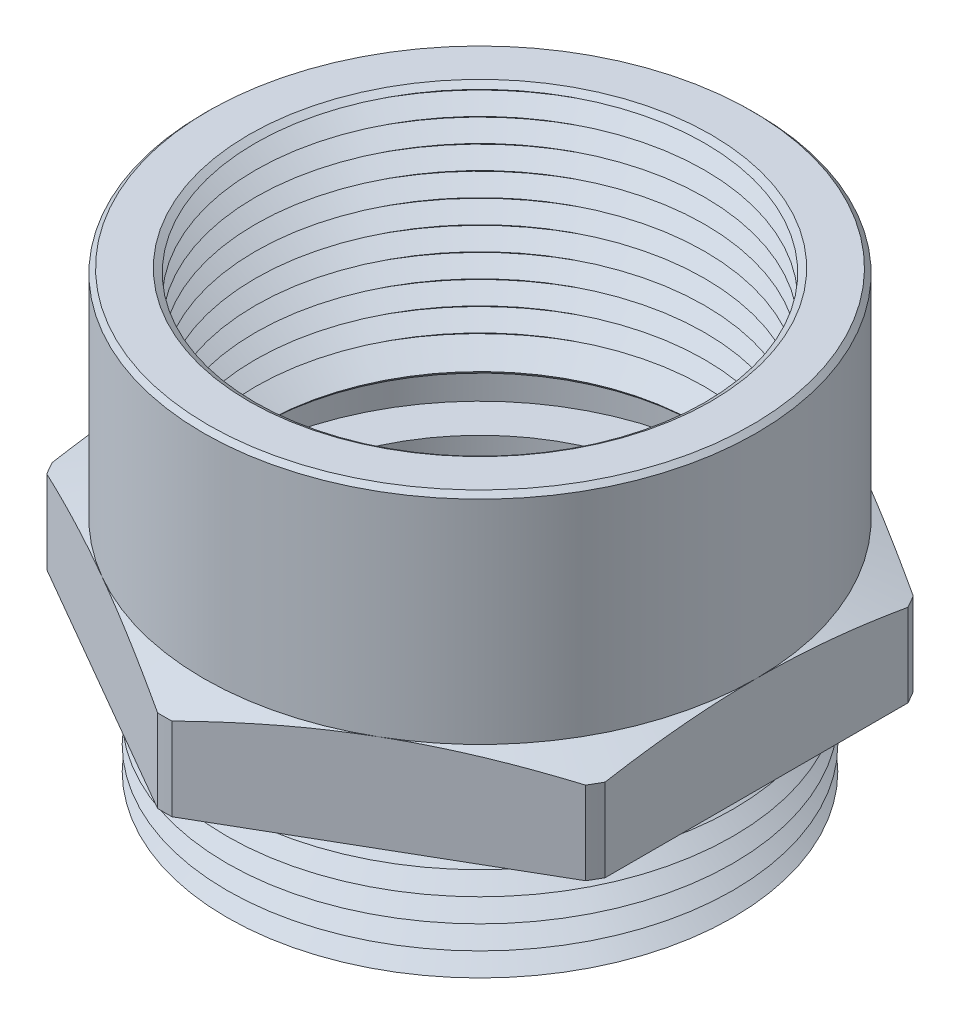
SolidWorks part; units mm, degrees
ref_plane "Front Plane" through (0, 0, 0) normal (0, 0, 1) x (1, 0, 0)
ref_plane "Top Plane" through (0, 0, 0) normal (0, 1, 0) x (1, 0, 0)
ref_plane "Right Plane" through (0, 0, 0) normal (1, 0, 0) x (0, 0, -1)
sketch "Sketch1" plane through (0, 0, 0) normal (0, 0, 1) x (1, 0, 0)
  line L0 (0, 0) -> (0, 68.999) construction
  line L1 (11.2776, 0) -> (13.9174, 0)
  line L2 (13.9174, 0) -> (14.097, 6.858)
  line L3 (14.097, 6.858) -> (17.084, 6.858)
  line L4 (17.084, 6.858) -> (17.084, 12.1107)
  line L5 (17.084, 12.1107) -> (14.986, 12.1107)
  line L6 (14.986, 12.1107) -> (14.986, 23.876)
  line L7 (14.986, 23.876) -> (12.1247, 23.876)
  line L8 (11.7729, 10.4394) -> (12.1247, 23.876)
  line L9 (11.7729, 10.4394) -> (13.5388, 10.4394)
  line L10 (13.5388, 10.4394) -> (13.5388, 8.0518)
  line L11 (13.5388, 8.0518) -> (11.2776, 8.0518)
  line L12 (11.2776, 8.0518) -> (11.2776, 0)
  dimension "D1" = 1.5
  dimension "D2" = 1.5
  dimension "A" = 28.194
  dimension "0.8A" = 22.5552
  dimension "B" = 23.5458
  dimension "T" = 6.858
  dimension "H" = 23.876
  dimension "0.22H" = 5.2527
  dimension "W1" = 34.1681
  dimension "1.1B" = 27.0777
  dimension "T+.05H" = 8.0518
  dimension "W" = 29.972
  dimension ".1H" = 2.3876
revolve "Revolve1" add sketch "Sketch1" angle 360 about L0
sketch "Sketch2" plane through (0, 6.858, 0) normal (0, -1, 0) x (1, 0, 0)
  line L1 (14.986, 8.6522) -> (0, 17.3043)
  line L2 (0, 17.3043) -> (-14.986, 8.6522)
  line L3 (-14.986, 8.6522) -> (-14.986, -8.6522)
  line L4 (-14.986, -8.6522) -> (0, -17.3043)
  line L5 (0, -17.3043) -> (14.986, -8.6522)
  line L6 (14.986, -8.6522) -> (14.986, 8.6522)
  circle A0 centre (0, 0) radius 14.986 construction
  dimension "Wr" = 29.972
extrude "Cut-Extrude1" cut sketch "Sketch2" against normal through all flip side to cut
sketch "Sketch4" plane through (0, 12.1107, 0) normal (0, 1, 0) x (-1, 0, 0)
  circle A0 centre (0, 0) radius 14.986 construction
  circle A1 centre (0, 0) radius 14.986
extrude "Cut-Extrude3" cut sketch "Sketch4" against normal blind 1.27 draft 70 flip side to cut
chamfer "Chamfer2" distance 0.254 angle 45 1 edges at (0, 10.4394, -11.7729)
sketch "Sketch7" plane through (0, 0, 0) normal (0, 0, 1) x (1, 0, 0)
  line L0 (-11.7794, 10.6869) -> (-11.8263, 12.4769)
  line L1 (-12.1247, 23.876) -> (-11.7794, 10.6869) construction
  line L2 (-11.8263, 12.4769) -> (-13.081, 11.5484)
  line L3 (-13.081, 11.5484) -> (-11.7794, 10.6869)
  line L4 (0, 0) -> (0, 27.6835) construction
  dimension "D1" = 55
  dimension "D2" = 55
  dimension "D3" = 26.162
revolve "Cut-Revolve1" cut sketch "Sketch7" angle 360 about L4
pattern_linear "LPattern1" count 11 spacing 1.27 along (0, 1, 0) of "Cut-Revolve1"
sketch "Sketch8" plane through (0, 0, 0) normal (0, 0, 1) x (1, 0, 0)
  line L0 (-14.097, 6.858) -> (-12.8042, 6.0023)
  line L1 (-12.8042, 6.0023) -> (-14.0504, 5.0801)
  line L2 (-14.097, 6.858) -> (-13.9174, 0) construction
  line L3 (-14.0504, 5.0801) -> (-14.097, 6.858)
  line L5 (0, 0) -> (0, 25.4984) construction
  dimension "D1" = 55
  dimension "D2" = 55
  dimension "D3" = 1.27
revolve "Cut-Revolve2" cut sketch "Sketch8" angle 360 about L5
pattern_linear "LPattern2" count 6 spacing 1.27 along (0, -1, 0) of "Cut-Revolve2"
chamfer "Chamfer3" distance 0.254 angle 45 1 edges at (0, 23.876, -14.986)
